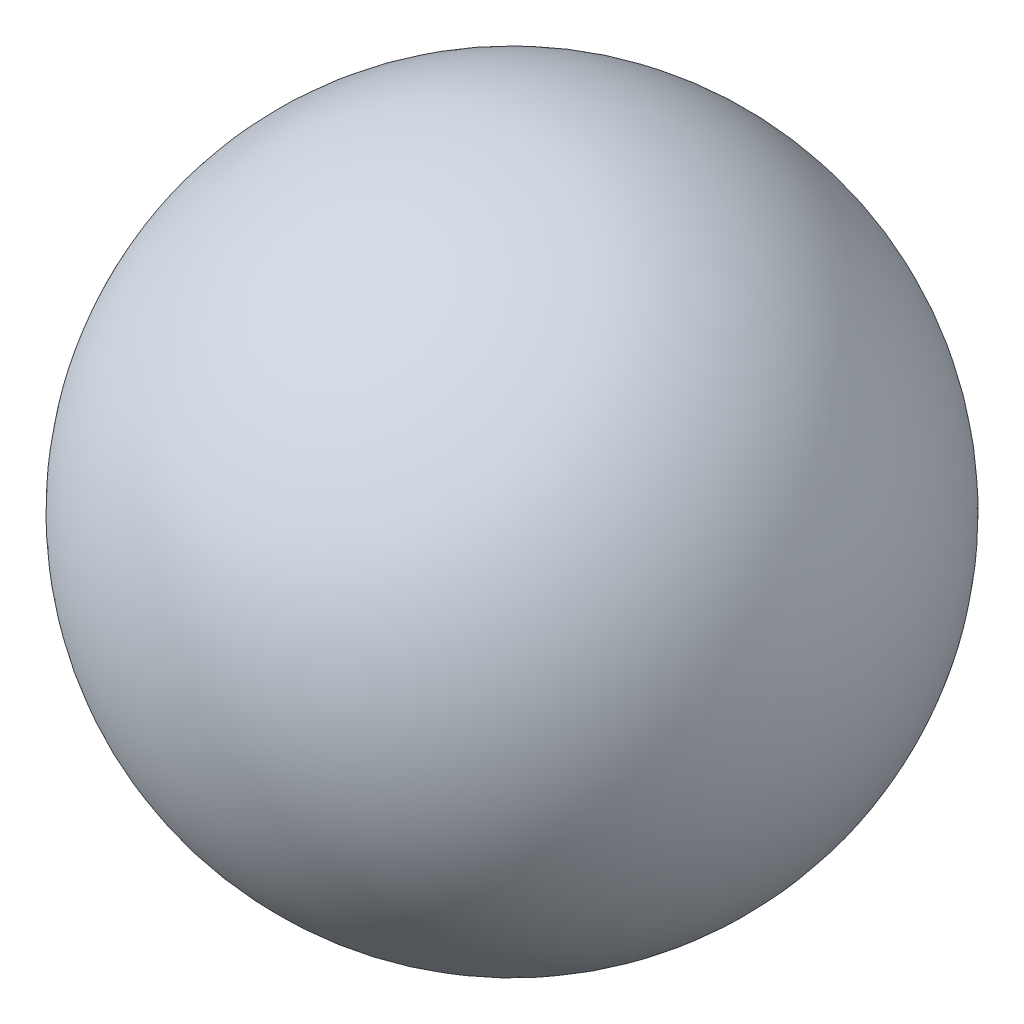
SolidWorks part; units mm, degrees
ref_plane "Front Plane" through (0, 0, 0) normal (0, 0, 1) x (1, 0, 0)
ref_plane "Top Plane" through (0, 0, 0) normal (0, 1, 0) x (1, 0, 0)
ref_plane "Right Plane" through (0, 0, 0) normal (1, 0, 0) x (0, 0, -1)
sketch "Sketch1" plane through (0, 0, 0) normal (0, 1, 0) x (1, 0, 0)
  line L0 (-15, 0) -> (15, 0)
  arc A0 (15, 0) -> (-15, 0) centre (0, 0) ccw
  dimension "D1" = 30
revolve "Revolve1" add sketch "Sketch1" angle 360 about L0
